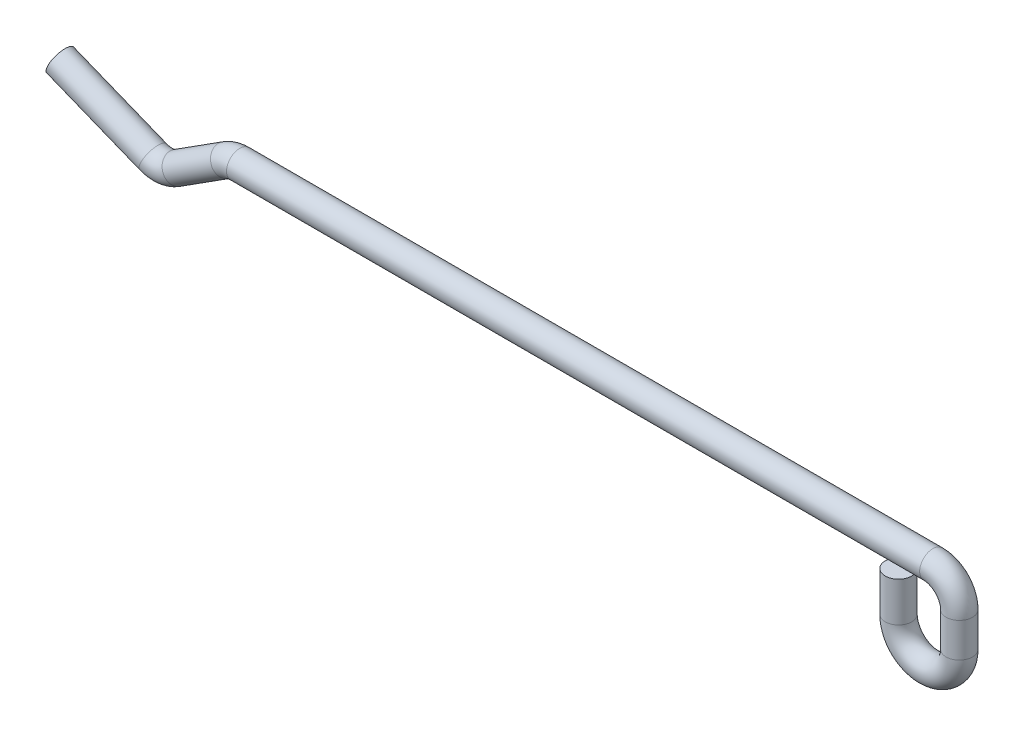
SolidWorks part; units mm, degrees
ref_plane "Face" through (0, 0, 0) normal (0, 0, 1) x (1, 0, 0)
ref_plane "Dessus" through (0, 0, 0) normal (0, 1, 0) x (1, 0, 0)
ref_plane "Droite" through (0, 0, 0) normal (1, 0, 0) x (0, 0, -1)
sketch "Esquisse1" plane through (0, 0, 0) normal (0, 0, 1) x (1, 0, 0)
  line L0 (4.6, -3) -> (4.6, -0.4)
  line L1 (2.6, 1.6) -> (-49.8165, 1.6)
  line L2 (-50.8919, 1.2863) -> (-54.5514, -1.0476)
  line L3 (-56.371, -1.2178) -> (-63.4, 1.6)
  line L4 (0, -3) -> (0, 0)
  arc A0 (0, -3) -> (4.6, -3) centre (2.3, -3) ccw
  arc A1 (4.6, -0.4) -> (2.6, 1.6) centre (2.6, -0.4) ccw
  arc A2 (-49.8165, 1.6) -> (-50.8919, 1.2863) centre (-49.8165, -0.4) ccw
  arc A3 (-54.5514, -1.0476) -> (-56.371, -1.2178) centre (-55.6268, 0.6386) cw
  point P11 (4.6, 1.6)
  point P14 (-50.4, 1.6)
  point P17 (-55.4175, -1.6)
  point P18 (2.3, -5.3)
  dimension "D1" = 2.3
  dimension "D8" = 2
  dimension "D2" = 4.6
  dimension "D3" = 55
  dimension "D4" = 68
  dimension "D5" = 8.6
  dimension "D6" = 3.2
  dimension "D7" = 3
sketch "Esquisse2" plane through (0, 0, 0) normal (0, 1, 0) x (1, 0, 0)
  circle A0 centre (0, 0) radius 1
  dimension "D1" = 2
sweep "Balayage1" add profiles "Esquisse2" path "Esquisse1"
